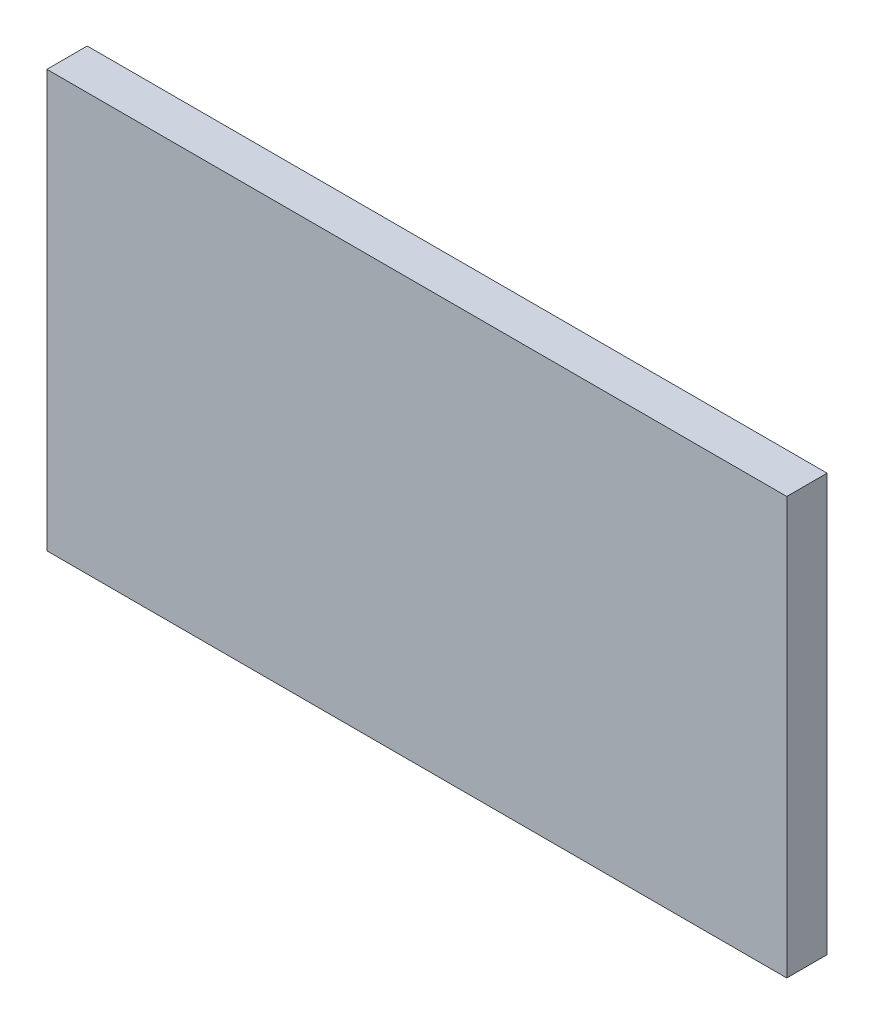
SolidWorks part; units mm, degrees
material "ABS PC"
ref_plane "Front Plane" through (0, 0, 0) normal (0, 0, 1) x (1, 0, 0)
ref_plane "Top Plane" through (0, 0, 0) normal (0, 1, 0) x (1, 0, 0)
ref_plane "Right Plane" through (0, 0, 0) normal (1, 0, 0) x (0, 0, -1)
sketch "Sketch1" plane through (0, 0, 0) normal (0, 0, 1) x (1, 0, 0)
  line L0 (113.8054, 85.5536) -> (113.8054, -262.279) construction
  line L4 (120.7904, -92.2997) -> (106.8204, -92.2997)
  line L5 (120.7904, -92.2997) -> (120.7904, -84.4257)
  line L6 (120.7904, -84.4257) -> (106.8204, -84.4257)
  line L7 (106.8204, -92.2997) -> (106.8204, -84.4257)
  line L8 (120.7904, -92.2997) -> (106.8204, -84.4257) construction
  line L9 (120.7904, -84.4257) -> (106.8204, -92.2997) construction
  line L15 (106.4394, -92.6807) -> (121.1714, -92.6807) construction
  line L16 (121.1714, -84.0447) -> (106.4394, -84.0447) construction
  line L17 (106.4394, -84.0447) -> (106.4394, -92.6807) construction
  line L18 (121.1714, -92.6807) -> (121.1714, -84.0447) construction
  point P6 (113.8054, -88.3627)
  dimension "D1" = 0.381
  dimension "D2" = 0.381
  dimension "D3" = 0.381
  dimension "D4" = 0.381
extrude "Boss-Extrude1" add sketch "Sketch1" along normal blind 0.762
equation "\"D2@Sketch1\"=\"D1@Sketch1\""
equation "\"D3@Sketch1\"=\"D1@Sketch1\""
equation "\"D4@Sketch1\"=\"D1@Sketch1\""
